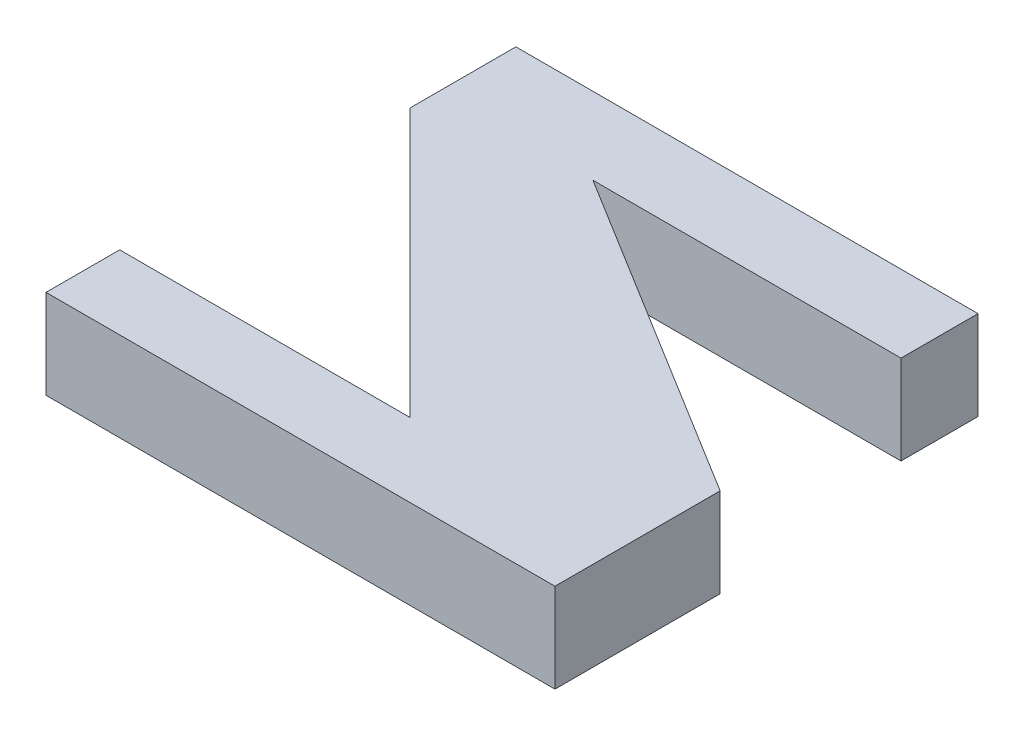
SolidWorks part; units mm, degrees
ref_plane "Front Plane" through (0, 0, 0) normal (0, 0, 1) x (1, 0, 0)
ref_plane "Top Plane" through (0, 0, 0) normal (0, 1, 0) x (1, 0, 0)
ref_plane "Right Plane" through (0, 0, 0) normal (1, 0, 0) x (0, 0, -1)
sketch "Sketch1" plane through (0, 0, 0) normal (0, 1, 0) x (1, 0, 0)
  line L0 (0, 0) -> (-51.8303, 0)
  line L1 (-51.8303, 0) -> (-51.8303, -11.8934)
  line L2 (-51.8303, -11.8934) -> (-21.7837, -41.9399)
  line L3 (-21.7837, -41.9399) -> (-54.3341, -41.9399)
  line L4 (-54.3341, -41.9399) -> (-54.3341, -50.2027)
  line L5 (-54.3341, -50.2027) -> (2.7543, -50.2027)
  line L6 (2.7543, -50.2027) -> (2.7543, -31.674)
  line L7 (2.7543, -31.674) -> (-34.5535, -8.6384)
  line L8 (-34.5535, -8.6384) -> (0, -8.6384)
  line L9 (0, -8.6384) -> (0, 0)
extrude "Boss-Extrude1" add sketch "Sketch1" along normal blind 10
